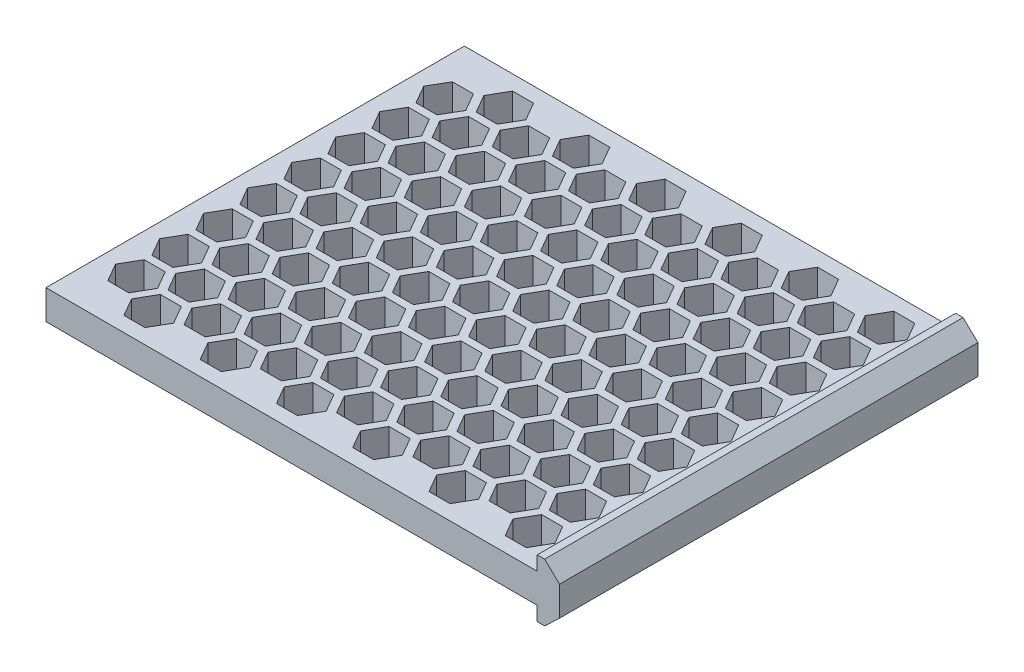
SolidWorks part; units mm, degrees
ref_plane "Front Plane" through (0, 0, 0) normal (0, 0, 1) x (1, 0, 0)
ref_plane "Top Plane" through (0, 0, 0) normal (0, 1, 0) x (1, 0, 0)
ref_plane "Right Plane" through (0, 0, 0) normal (1, 0, 0) x (0, 0, -1)
sketch "Sketch1" plane through (0, 0, 0) normal (0, 0, 1) x (1, 0, 0)
  line L0 (0, 4.05) -> (-140, 4.05)
  line L1 (0, -4.05) -> (-140, -4.05)
  line L2 (-140, -4.05) -> (-140, 4.05)
  line B0 (0, 7.95) -> (2.04, 7.95)
  line B1 (6.1524, 4.048) -> (6.1524, -4.048)
  line B2 (2.04, -7.95) -> (0, -7.95)
  line B3 (0, -7.95) -> (0, 7.95)
  line B4 (2.04, 7.95) -> (6.1524, 4.048)
  line B5 (6.1524, -4.048) -> (2.04, -7.95)
  line B6 (0, 4.05) -> (0, -4.05) construction
  dimension "D1" = 140
sketch_block_instance "Extrusion Profile-2"
sketch_block "Extrusion Profile" parameters "D1"=8.44, "D2"=2.6, "D3"=6, "D4"=16.7, "D6"=5.6686, "D7"=2.0404, "D8"=8.0963, "D9"=15.9, "D5"=2.4157
extrude "Boss-Extrude1" add sketch "Sketch1" along normal blind 115 contours L1 B3 L0 L2 | B2 B5 B1 B4 B0 B3
sketch "Sketch2" plane through (0, 4.05, 0) normal (0, 1, 0) x (1, 0, 0)
  line L0 (-16.1488, -12.65) -> (-14.3301, -11.6) construction
  line L1 (-4.2265, -9.1) -> (-7.1132, -4.1)
  line L2 (-7.1132, -4.1) -> (-12.8868, -4.1)
  line L3 (-12.8868, -4.1) -> (-15.7735, -9.1)
  line L4 (-15.7735, -9.1) -> (-12.8868, -14.1)
  line L5 (-12.8868, -14.1) -> (-7.1132, -14.1)
  line L6 (-7.1132, -14.1) -> (-4.2265, -9.1)
  line L7 (0, -115) -> (0, 0) construction
  line L8 (-4.2265, -21.2) -> (-7.1132, -16.2)
  line L9 (-7.1132, -16.2) -> (-12.8868, -16.2)
  line L10 (-12.8868, -16.2) -> (-15.7735, -21.2)
  line L11 (-15.7735, -21.2) -> (-12.8868, -26.2)
  line L12 (-12.8868, -26.2) -> (-7.1132, -26.2)
  line L13 (-7.1132, -26.2) -> (-4.2265, -21.2)
  line L14 (-4.2265, -33.3) -> (-7.1132, -28.3)
  line L15 (-7.1132, -28.3) -> (-12.8868, -28.3)
  line L16 (-12.8868, -28.3) -> (-15.7735, -33.3)
  line L17 (-15.7735, -33.3) -> (-12.8868, -38.3)
  line L18 (-12.8868, -38.3) -> (-7.1132, -38.3)
  line L19 (-7.1132, -38.3) -> (-4.2265, -33.3)
  line L20 (-4.2265, -45.4) -> (-7.1132, -40.4)
  line L21 (-7.1132, -40.4) -> (-12.8868, -40.4)
  line L22 (-12.8868, -40.4) -> (-15.7735, -45.4)
  line L23 (-15.7735, -45.4) -> (-12.8868, -50.4)
  line L24 (-12.8868, -50.4) -> (-7.1132, -50.4)
  line L25 (-7.1132, -50.4) -> (-4.2265, -45.4)
  line L26 (-4.2265, -57.5) -> (-7.1132, -52.5)
  line L27 (-7.1132, -52.5) -> (-12.8868, -52.5)
  line L28 (-12.8868, -52.5) -> (-15.7735, -57.5)
  line L29 (-15.7735, -57.5) -> (-12.8868, -62.5)
  line L30 (-12.8868, -62.5) -> (-7.1132, -62.5)
  line L31 (-7.1132, -62.5) -> (-4.2265, -57.5)
  line L32 (-4.2265, -69.6) -> (-7.1132, -64.6)
  line L33 (-7.1132, -64.6) -> (-12.8868, -64.6)
  line L34 (-12.8868, -64.6) -> (-15.7735, -69.6)
  line L35 (-15.7735, -69.6) -> (-12.8868, -74.6)
  line L36 (-12.8868, -74.6) -> (-7.1132, -74.6)
  line L37 (-7.1132, -74.6) -> (-4.2265, -69.6)
  line L38 (-4.2265, -81.7) -> (-7.1132, -76.7)
  line L39 (-7.1132, -76.7) -> (-12.8868, -76.7)
  line L40 (-12.8868, -76.7) -> (-15.7735, -81.7)
  line L41 (-15.7735, -81.7) -> (-12.8868, -86.7)
  line L42 (-12.8868, -86.7) -> (-7.1132, -86.7)
  line L43 (-7.1132, -86.7) -> (-4.2265, -81.7)
  line L44 (-4.2265, -93.8) -> (-7.1132, -88.8)
  line L45 (-7.1132, -88.8) -> (-12.8868, -88.8)
  line L46 (-12.8868, -88.8) -> (-15.7735, -93.8)
  line L47 (-15.7735, -93.8) -> (-12.8868, -98.8)
  line L48 (-12.8868, -98.8) -> (-7.1132, -98.8)
  line L49 (-7.1132, -98.8) -> (-4.2265, -93.8)
  line L50 (-4.2265, -105.9) -> (-7.1132, -100.9)
  line L51 (-7.1132, -100.9) -> (-12.8868, -100.9)
  line L52 (-12.8868, -100.9) -> (-15.7735, -105.9)
  line L53 (-15.7735, -105.9) -> (-12.8868, -110.9)
  line L54 (-12.8868, -110.9) -> (-7.1132, -110.9)
  line L55 (-7.1132, -110.9) -> (-4.2265, -105.9)
  line L56 (-14.7054, -15.15) -> (-17.5922, -10.15)
  line L57 (-17.5922, -10.15) -> (-23.3657, -10.15)
  line L58 (-23.3657, -10.15) -> (-26.2524, -15.15)
  line L59 (-10, -4.1) -> (-10, 0) construction
  line L60 (0, 0) -> (-140, 0) construction
  line L61 (-10, -110.9) -> (-10, -115) construction
  line L62 (-26.2524, -15.15) -> (-23.3657, -20.15)
  line L69 (-4.2265, -118) -> (-7.1132, -113) [skipped]
  line L70 (-7.1132, -113) -> (-12.8868, -113) [skipped]
  line L71 (-12.8868, -113) -> (-15.7735, -118) [skipped]
  line L72 (-15.7735, -118) -> (-12.8868, -123) [skipped]
  line L73 (-12.8868, -123) -> (-7.1132, -123) [skipped]
  line L74 (-7.1132, -123) -> (-4.2265, -118) [skipped]
  line L75 (0, -115) -> (-140, -115) construction
  line L76 (-23.3657, -20.15) -> (-17.5922, -20.15)
  line L77 (-17.5922, -20.15) -> (-14.7054, -15.15)
  line L79 (-16.1488, -17.65) -> (-14.3301, -18.7) construction
  line L81 (-10, -14.1) -> (-10, -16.2) construction
  line L83 (-14.7054, -27.25) -> (-17.5922, -22.25)
  line L84 (-17.5922, -22.25) -> (-23.3657, -22.25)
  line L85 (-23.3657, -22.25) -> (-26.2524, -27.25)
  line L86 (-26.2524, -27.25) -> (-23.3657, -32.25)
  line L87 (-23.3657, -32.25) -> (-17.5922, -32.25)
  line L88 (-17.5922, -32.25) -> (-14.7054, -27.25)
  line L89 (-14.7054, -39.35) -> (-17.5922, -34.35)
  line L90 (-17.5922, -34.35) -> (-23.3657, -34.35)
  line L91 (-23.3657, -34.35) -> (-26.2524, -39.35)
  line L92 (-26.2524, -39.35) -> (-23.3657, -44.35)
  line L93 (-23.3657, -44.35) -> (-17.5922, -44.35)
  line L94 (-17.5922, -44.35) -> (-14.7054, -39.35)
  line L95 (-14.7054, -51.45) -> (-17.5922, -46.45)
  line L96 (-17.5922, -46.45) -> (-23.3657, -46.45)
  line L97 (-23.3657, -46.45) -> (-26.2524, -51.45)
  line L98 (-26.2524, -51.45) -> (-23.3657, -56.45)
  line L99 (-23.3657, -56.45) -> (-17.5922, -56.45)
  line L100 (-17.5922, -56.45) -> (-14.7054, -51.45)
  line L101 (-14.7054, -63.55) -> (-17.5922, -58.55)
  line L102 (-17.5922, -58.55) -> (-23.3657, -58.55)
  line L103 (-23.3657, -58.55) -> (-26.2524, -63.55)
  line L104 (-26.2524, -63.55) -> (-23.3657, -68.55)
  line L105 (-23.3657, -68.55) -> (-17.5922, -68.55)
  line L106 (-17.5922, -68.55) -> (-14.7054, -63.55)
  line L107 (-14.7054, -75.65) -> (-17.5922, -70.65)
  line L108 (-17.5922, -70.65) -> (-23.3657, -70.65)
  line L109 (-23.3657, -70.65) -> (-26.2524, -75.65)
  line L110 (-26.2524, -75.65) -> (-23.3657, -80.65)
  line L111 (-23.3657, -80.65) -> (-17.5922, -80.65)
  line L112 (-17.5922, -80.65) -> (-14.7054, -75.65)
  line L113 (-14.7054, -87.75) -> (-17.5922, -82.75)
  line L114 (-17.5922, -82.75) -> (-23.3657, -82.75)
  line L115 (-23.3657, -82.75) -> (-26.2524, -87.75)
  line L116 (-26.2524, -87.75) -> (-23.3657, -92.75)
  line L117 (-23.3657, -92.75) -> (-17.5922, -92.75)
  line L118 (-17.5922, -92.75) -> (-14.7054, -87.75)
  line L119 (-14.7054, -99.85) -> (-17.5922, -94.85)
  line L120 (-17.5922, -94.85) -> (-23.3657, -94.85)
  line L121 (-23.3657, -94.85) -> (-26.2524, -99.85)
  line L122 (-26.2524, -99.85) -> (-23.3657, -104.85)
  line L123 (-23.3657, -104.85) -> (-17.5922, -104.85)
  line L124 (-17.5922, -104.85) -> (-14.7054, -99.85)
  line L125 (-14.7054, -15.15) -> (-14.7054, -27.25) construction
  line L126 (-25.1843, -9.1) -> (-28.0711, -4.1)
  line L127 (-28.0711, -4.1) -> (-33.8446, -4.1)
  line L128 (-33.8446, -4.1) -> (-36.7313, -9.1)
  line L129 (-36.7313, -9.1) -> (-33.8446, -14.1)
  line L130 (-33.8446, -14.1) -> (-28.0711, -14.1)
  line L131 (-28.0711, -14.1) -> (-25.1843, -9.1)
  line L132 (-25.1843, -21.2) -> (-28.0711, -16.2)
  line L133 (-28.0711, -16.2) -> (-33.8446, -16.2)
  line L134 (-33.8446, -16.2) -> (-36.7313, -21.2)
  line L135 (-36.7313, -21.2) -> (-33.8446, -26.2)
  line L136 (-33.8446, -26.2) -> (-28.0711, -26.2)
  line L137 (-28.0711, -26.2) -> (-25.1843, -21.2)
  line L138 (-25.1843, -33.3) -> (-28.0711, -28.3)
  line L139 (-28.0711, -28.3) -> (-33.8446, -28.3)
  line L140 (-33.8446, -28.3) -> (-36.7313, -33.3)
  line L141 (-36.7313, -33.3) -> (-33.8446, -38.3)
  line L142 (-33.8446, -38.3) -> (-28.0711, -38.3)
  line L143 (-28.0711, -38.3) -> (-25.1843, -33.3)
  line L144 (-25.1843, -45.4) -> (-28.0711, -40.4)
  line L145 (-28.0711, -40.4) -> (-33.8446, -40.4)
  line L146 (-33.8446, -40.4) -> (-36.7313, -45.4)
  line L147 (-36.7313, -45.4) -> (-33.8446, -50.4)
  line L148 (-33.8446, -50.4) -> (-28.0711, -50.4)
  line L149 (-28.0711, -50.4) -> (-25.1843, -45.4)
  line L150 (-25.1843, -57.5) -> (-28.0711, -52.5)
  line L151 (-28.0711, -52.5) -> (-33.8446, -52.5)
  line L152 (-33.8446, -52.5) -> (-36.7313, -57.5)
  line L153 (-36.7313, -57.5) -> (-33.8446, -62.5)
  line L154 (-33.8446, -62.5) -> (-28.0711, -62.5)
  line L155 (-28.0711, -62.5) -> (-25.1843, -57.5)
  line L156 (-25.1843, -69.6) -> (-28.0711, -64.6)
  line L157 (-28.0711, -64.6) -> (-33.8446, -64.6)
  line L158 (-33.8446, -64.6) -> (-36.7313, -69.6)
  line L159 (-36.7313, -69.6) -> (-33.8446, -74.6)
  line L160 (-33.8446, -74.6) -> (-28.0711, -74.6)
  line L161 (-28.0711, -74.6) -> (-25.1843, -69.6)
  line L162 (-25.1843, -81.7) -> (-28.0711, -76.7)
  line L163 (-28.0711, -76.7) -> (-33.8446, -76.7)
  line L164 (-33.8446, -76.7) -> (-36.7313, -81.7)
  line L165 (-36.7313, -81.7) -> (-33.8446, -86.7)
  line L166 (-33.8446, -86.7) -> (-28.0711, -86.7)
  line L167 (-28.0711, -86.7) -> (-25.1843, -81.7)
  line L168 (-25.1843, -93.8) -> (-28.0711, -88.8)
  line L169 (-28.0711, -88.8) -> (-33.8446, -88.8)
  line L170 (-33.8446, -88.8) -> (-36.7313, -93.8)
  line L171 (-36.7313, -93.8) -> (-33.8446, -98.8)
  line L172 (-33.8446, -98.8) -> (-28.0711, -98.8)
  line L173 (-28.0711, -98.8) -> (-25.1843, -93.8)
  line L174 (-25.1843, -105.9) -> (-28.0711, -100.9)
  line L175 (-28.0711, -100.9) -> (-33.8446, -100.9)
  line L176 (-33.8446, -100.9) -> (-36.7313, -105.9)
  line L177 (-36.7313, -105.9) -> (-33.8446, -110.9)
  line L178 (-33.8446, -110.9) -> (-28.0711, -110.9)
  line L179 (-28.0711, -110.9) -> (-25.1843, -105.9)
  line L180 (-35.6632, -15.15) -> (-38.55, -10.15)
  line L181 (-38.55, -10.15) -> (-44.3235, -10.15)
  line L182 (-44.3235, -10.15) -> (-47.2102, -15.15)
  line L183 (-47.2102, -15.15) -> (-44.3235, -20.15)
  line L184 (-44.3235, -20.15) -> (-38.55, -20.15)
  line L185 (-38.55, -20.15) -> (-35.6632, -15.15)
  line L186 (-35.6632, -27.25) -> (-38.55, -22.25)
  line L187 (-38.55, -22.25) -> (-44.3235, -22.25)
  line L188 (-44.3235, -22.25) -> (-47.2102, -27.25)
  line L189 (-47.2102, -27.25) -> (-44.3235, -32.25)
  line L190 (-44.3235, -32.25) -> (-38.55, -32.25)
  line L191 (-38.55, -32.25) -> (-35.6632, -27.25)
  line L192 (-35.6632, -39.35) -> (-38.55, -34.35)
  line L193 (-38.55, -34.35) -> (-44.3235, -34.35)
  line L194 (-44.3235, -34.35) -> (-47.2102, -39.35)
  line L195 (-47.2102, -39.35) -> (-44.3235, -44.35)
  line L196 (-44.3235, -44.35) -> (-38.55, -44.35)
  line L197 (-38.55, -44.35) -> (-35.6632, -39.35)
  line L198 (-35.6632, -51.45) -> (-38.55, -46.45)
  line L199 (-38.55, -46.45) -> (-44.3235, -46.45)
  line L200 (-44.3235, -46.45) -> (-47.2102, -51.45)
  line L201 (-47.2102, -51.45) -> (-44.3235, -56.45)
  line L202 (-44.3235, -56.45) -> (-38.55, -56.45)
  line L203 (-38.55, -56.45) -> (-35.6632, -51.45)
  line L204 (-35.6632, -63.55) -> (-38.55, -58.55)
  line L205 (-38.55, -58.55) -> (-44.3235, -58.55)
  line L206 (-44.3235, -58.55) -> (-47.2102, -63.55)
  line L207 (-47.2102, -63.55) -> (-44.3235, -68.55)
  line L208 (-44.3235, -68.55) -> (-38.55, -68.55)
  line L209 (-38.55, -68.55) -> (-35.6632, -63.55)
  line L210 (-35.6632, -75.65) -> (-38.55, -70.65)
  line L211 (-38.55, -70.65) -> (-44.3235, -70.65)
  line L212 (-44.3235, -70.65) -> (-47.2102, -75.65)
  line L213 (-47.2102, -75.65) -> (-44.3235, -80.65)
  line L214 (-44.3235, -80.65) -> (-38.55, -80.65)
  line L215 (-38.55, -80.65) -> (-35.6632, -75.65)
  line L216 (-35.6632, -87.75) -> (-38.55, -82.75)
  line L217 (-38.55, -82.75) -> (-44.3235, -82.75)
  line L218 (-44.3235, -82.75) -> (-47.2102, -87.75)
  line L219 (-47.2102, -87.75) -> (-44.3235, -92.75)
  line L220 (-44.3235, -92.75) -> (-38.55, -92.75)
  line L221 (-38.55, -92.75) -> (-35.6632, -87.75)
  line L222 (-35.6632, -99.85) -> (-38.55, -94.85)
  line L223 (-38.55, -94.85) -> (-44.3235, -94.85)
  line L224 (-44.3235, -94.85) -> (-47.2102, -99.85)
  line L225 (-47.2102, -99.85) -> (-44.3235, -104.85)
  line L226 (-44.3235, -104.85) -> (-38.55, -104.85)
  line L227 (-38.55, -104.85) -> (-35.6632, -99.85)
  line L228 (-37.1066, -12.65) -> (-35.2879, -11.6) construction
  line L229 (-30.9578, -4.1) -> (-30.9578, 0) construction
  line L230 (-30.9578, -110.9) -> (-30.9578, -115) construction
  line L231 (-37.1066, -17.65) -> (-35.2879, -18.7) construction
  line L232 (-30.9578, -15.15) -> (-30.9578, -14.1)
  line L233 (-35.6632, -15.15) -> (-35.6632, -27.25) construction
  line L234 (-46.1421, -9.1) -> (-49.0289, -4.1)
  line L235 (-49.0289, -4.1) -> (-54.8024, -4.1)
  line L236 (-54.8024, -4.1) -> (-57.6891, -9.1)
  line L237 (-57.6891, -9.1) -> (-54.8024, -14.1)
  line L238 (-54.8024, -14.1) -> (-49.0289, -14.1)
  line L239 (-49.0289, -14.1) -> (-46.1421, -9.1)
  line L240 (-46.1421, -21.2) -> (-49.0289, -16.2)
  line L241 (-49.0289, -16.2) -> (-54.8024, -16.2)
  line L242 (-54.8024, -16.2) -> (-57.6891, -21.2)
  line L243 (-57.6891, -21.2) -> (-54.8024, -26.2)
  line L244 (-54.8024, -26.2) -> (-49.0289, -26.2)
  line L245 (-49.0289, -26.2) -> (-46.1421, -21.2)
  line L246 (-46.1421, -33.3) -> (-49.0289, -28.3)
  line L247 (-49.0289, -28.3) -> (-54.8024, -28.3)
  line L248 (-54.8024, -28.3) -> (-57.6891, -33.3)
  line L249 (-57.6891, -33.3) -> (-54.8024, -38.3)
  line L250 (-54.8024, -38.3) -> (-49.0289, -38.3)
  line L251 (-49.0289, -38.3) -> (-46.1421, -33.3)
  line L252 (-46.1421, -45.4) -> (-49.0289, -40.4)
  line L253 (-49.0289, -40.4) -> (-54.8024, -40.4)
  line L254 (-54.8024, -40.4) -> (-57.6891, -45.4)
  line L255 (-57.6891, -45.4) -> (-54.8024, -50.4)
  line L256 (-54.8024, -50.4) -> (-49.0289, -50.4)
  line L257 (-49.0289, -50.4) -> (-46.1421, -45.4)
  line L258 (-46.1421, -57.5) -> (-49.0289, -52.5)
  line L259 (-49.0289, -52.5) -> (-54.8024, -52.5)
  line L260 (-54.8024, -52.5) -> (-57.6891, -57.5)
  line L261 (-57.6891, -57.5) -> (-54.8024, -62.5)
  line L262 (-54.8024, -62.5) -> (-49.0289, -62.5)
  line L263 (-49.0289, -62.5) -> (-46.1421, -57.5)
  line L264 (-46.1421, -69.6) -> (-49.0289, -64.6)
  line L265 (-49.0289, -64.6) -> (-54.8024, -64.6)
  line L266 (-54.8024, -64.6) -> (-57.6891, -69.6)
  line L267 (-57.6891, -69.6) -> (-54.8024, -74.6)
  line L268 (-54.8024, -74.6) -> (-49.0289, -74.6)
  line L269 (-49.0289, -74.6) -> (-46.1421, -69.6)
  line L270 (-46.1421, -81.7) -> (-49.0289, -76.7)
  line L271 (-49.0289, -76.7) -> (-54.8024, -76.7)
  line L272 (-54.8024, -76.7) -> (-57.6891, -81.7)
  line L273 (-57.6891, -81.7) -> (-54.8024, -86.7)
  line L274 (-54.8024, -86.7) -> (-49.0289, -86.7)
  line L275 (-49.0289, -86.7) -> (-46.1421, -81.7)
  line L276 (-46.1421, -93.8) -> (-49.0289, -88.8)
  line L277 (-49.0289, -88.8) -> (-54.8024, -88.8)
  line L278 (-54.8024, -88.8) -> (-57.6891, -93.8)
  line L279 (-57.6891, -93.8) -> (-54.8024, -98.8)
  line L280 (-54.8024, -98.8) -> (-49.0289, -98.8)
  line L281 (-49.0289, -98.8) -> (-46.1421, -93.8)
  line L282 (-46.1421, -105.9) -> (-49.0289, -100.9)
  line L283 (-49.0289, -100.9) -> (-54.8024, -100.9)
  line L284 (-54.8024, -100.9) -> (-57.6891, -105.9)
  line L285 (-57.6891, -105.9) -> (-54.8024, -110.9)
  line L286 (-54.8024, -110.9) -> (-49.0289, -110.9)
  line L287 (-49.0289, -110.9) -> (-46.1421, -105.9)
  line L288 (-56.621, -15.15) -> (-59.5078, -10.15)
  line L289 (-59.5078, -10.15) -> (-65.2813, -10.15)
  line L290 (-65.2813, -10.15) -> (-68.168, -15.15)
  line L291 (-68.168, -15.15) -> (-65.2813, -20.15)
  line L292 (-65.2813, -20.15) -> (-59.5078, -20.15)
  line L293 (-59.5078, -20.15) -> (-56.621, -15.15)
  line L294 (-56.621, -27.25) -> (-59.5078, -22.25)
  line L295 (-59.5078, -22.25) -> (-65.2813, -22.25)
  line L296 (-65.2813, -22.25) -> (-68.168, -27.25)
  line L297 (-68.168, -27.25) -> (-65.2813, -32.25)
  line L298 (-65.2813, -32.25) -> (-59.5078, -32.25)
  line L299 (-59.5078, -32.25) -> (-56.621, -27.25)
  line L300 (-56.621, -39.35) -> (-59.5078, -34.35)
  line L301 (-59.5078, -34.35) -> (-65.2813, -34.35)
  line L302 (-65.2813, -34.35) -> (-68.168, -39.35)
  line L303 (-68.168, -39.35) -> (-65.2813, -44.35)
  line L304 (-65.2813, -44.35) -> (-59.5078, -44.35)
  line L305 (-59.5078, -44.35) -> (-56.621, -39.35)
  line L306 (-56.621, -51.45) -> (-59.5078, -46.45)
  line L307 (-59.5078, -46.45) -> (-65.2813, -46.45)
  line L308 (-65.2813, -46.45) -> (-68.168, -51.45)
  line L309 (-68.168, -51.45) -> (-65.2813, -56.45)
  line L310 (-65.2813, -56.45) -> (-59.5078, -56.45)
  line L311 (-59.5078, -56.45) -> (-56.621, -51.45)
  line L312 (-56.621, -63.55) -> (-59.5078, -58.55)
  line L313 (-59.5078, -58.55) -> (-65.2813, -58.55)
  line L314 (-65.2813, -58.55) -> (-68.168, -63.55)
  line L315 (-68.168, -63.55) -> (-65.2813, -68.55)
  line L316 (-65.2813, -68.55) -> (-59.5078, -68.55)
  line L317 (-59.5078, -68.55) -> (-56.621, -63.55)
  line L318 (-56.621, -75.65) -> (-59.5078, -70.65)
  line L319 (-59.5078, -70.65) -> (-65.2813, -70.65)
  line L320 (-65.2813, -70.65) -> (-68.168, -75.65)
  line L321 (-68.168, -75.65) -> (-65.2813, -80.65)
  line L322 (-65.2813, -80.65) -> (-59.5078, -80.65)
  line L323 (-59.5078, -80.65) -> (-56.621, -75.65)
  line L324 (-56.621, -87.75) -> (-59.5078, -82.75)
  line L325 (-59.5078, -82.75) -> (-65.2813, -82.75)
  line L326 (-65.2813, -82.75) -> (-68.168, -87.75)
  line L327 (-68.168, -87.75) -> (-65.2813, -92.75)
  line L328 (-65.2813, -92.75) -> (-59.5078, -92.75)
  line L329 (-59.5078, -92.75) -> (-56.621, -87.75)
  line L330 (-56.621, -99.85) -> (-59.5078, -94.85)
  line L331 (-59.5078, -94.85) -> (-65.2813, -94.85)
  line L332 (-65.2813, -94.85) -> (-68.168, -99.85)
  line L333 (-68.168, -99.85) -> (-65.2813, -104.85)
  line L334 (-65.2813, -104.85) -> (-59.5078, -104.85)
  line L335 (-59.5078, -104.85) -> (-56.621, -99.85)
  line L336 (-58.0644, -12.65) -> (-56.2458, -11.6) construction
  line L337 (-51.9156, -4.1) -> (-51.9156, 0) construction
  line L338 (-51.9156, -110.9) -> (-51.9156, -115) construction
  line L339 (-58.0644, -17.65) -> (-56.2458, -18.7) construction
  line L340 (-51.9156, -14.1) -> (-51.9156, -16.2) construction
  line L341 (-56.621, -15.15) -> (-56.621, -27.25) construction
  line L342 (-67.0999, -9.1) -> (-69.9867, -4.1)
  line L343 (-69.9867, -4.1) -> (-75.7602, -4.1)
  line L344 (-75.7602, -4.1) -> (-78.6469, -9.1)
  line L345 (-78.6469, -9.1) -> (-75.7602, -14.1)
  line L346 (-75.7602, -14.1) -> (-69.9867, -14.1)
  line L347 (-69.9867, -14.1) -> (-67.0999, -9.1)
  line L348 (-67.0999, -21.2) -> (-69.9867, -16.2)
  line L349 (-69.9867, -16.2) -> (-75.7602, -16.2)
  line L350 (-75.7602, -16.2) -> (-78.6469, -21.2)
  line L351 (-78.6469, -21.2) -> (-75.7602, -26.2)
  line L352 (-75.7602, -26.2) -> (-69.9867, -26.2)
  line L353 (-69.9867, -26.2) -> (-67.0999, -21.2)
  line L354 (-67.0999, -33.3) -> (-69.9867, -28.3)
  line L355 (-69.9867, -28.3) -> (-75.7602, -28.3)
  line L356 (-75.7602, -28.3) -> (-78.6469, -33.3)
  line L357 (-78.6469, -33.3) -> (-75.7602, -38.3)
  line L358 (-75.7602, -38.3) -> (-69.9867, -38.3)
  line L359 (-69.9867, -38.3) -> (-67.0999, -33.3)
  line L360 (-67.0999, -45.4) -> (-69.9867, -40.4)
  line L361 (-69.9867, -40.4) -> (-75.7602, -40.4)
  line L362 (-75.7602, -40.4) -> (-78.6469, -45.4)
  line L363 (-78.6469, -45.4) -> (-75.7602, -50.4)
  line L364 (-75.7602, -50.4) -> (-69.9867, -50.4)
  line L365 (-69.9867, -50.4) -> (-67.0999, -45.4)
  line L366 (-67.0999, -57.5) -> (-69.9867, -52.5)
  line L367 (-69.9867, -52.5) -> (-75.7602, -52.5)
  line L368 (-75.7602, -52.5) -> (-78.6469, -57.5)
  line L369 (-78.6469, -57.5) -> (-75.7602, -62.5)
  line L370 (-75.7602, -62.5) -> (-69.9867, -62.5)
  line L371 (-69.9867, -62.5) -> (-67.0999, -57.5)
  line L372 (-67.0999, -69.6) -> (-69.9867, -64.6)
  line L373 (-69.9867, -64.6) -> (-75.7602, -64.6)
  line L374 (-75.7602, -64.6) -> (-78.6469, -69.6)
  line L375 (-78.6469, -69.6) -> (-75.7602, -74.6)
  line L376 (-75.7602, -74.6) -> (-69.9867, -74.6)
  line L377 (-69.9867, -74.6) -> (-67.0999, -69.6)
  line L378 (-67.0999, -81.7) -> (-69.9867, -76.7)
  line L379 (-69.9867, -76.7) -> (-75.7602, -76.7)
  line L380 (-75.7602, -76.7) -> (-78.6469, -81.7)
  line L381 (-78.6469, -81.7) -> (-75.7602, -86.7)
  line L382 (-75.7602, -86.7) -> (-69.9867, -86.7)
  line L383 (-69.9867, -86.7) -> (-67.0999, -81.7)
  line L384 (-67.0999, -93.8) -> (-69.9867, -88.8)
  line L385 (-69.9867, -88.8) -> (-75.7602, -88.8)
  line L386 (-75.7602, -88.8) -> (-78.6469, -93.8)
  line L387 (-78.6469, -93.8) -> (-75.7602, -98.8)
  line L388 (-75.7602, -98.8) -> (-69.9867, -98.8)
  line L389 (-69.9867, -98.8) -> (-67.0999, -93.8)
  line L390 (-67.0999, -105.9) -> (-69.9867, -100.9)
  line L391 (-69.9867, -100.9) -> (-75.7602, -100.9)
  line L392 (-75.7602, -100.9) -> (-78.6469, -105.9)
  line L393 (-78.6469, -105.9) -> (-75.7602, -110.9)
  line L394 (-75.7602, -110.9) -> (-69.9867, -110.9)
  line L395 (-69.9867, -110.9) -> (-67.0999, -105.9)
  line L396 (-77.5788, -15.15) -> (-80.4656, -10.15)
  line L397 (-80.4656, -10.15) -> (-86.2391, -10.15)
  line L398 (-86.2391, -10.15) -> (-89.1259, -15.15)
  line L399 (-89.1259, -15.15) -> (-86.2391, -20.15)
  line L400 (-86.2391, -20.15) -> (-80.4656, -20.15)
  line L401 (-80.4656, -20.15) -> (-77.5788, -15.15)
  line L402 (-77.5788, -27.25) -> (-80.4656, -22.25)
  line L403 (-80.4656, -22.25) -> (-86.2391, -22.25)
  line L404 (-86.2391, -22.25) -> (-89.1259, -27.25)
  line L405 (-89.1259, -27.25) -> (-86.2391, -32.25)
  line L406 (-86.2391, -32.25) -> (-80.4656, -32.25)
  line L407 (-80.4656, -32.25) -> (-77.5788, -27.25)
  line L408 (-77.5788, -39.35) -> (-80.4656, -34.35)
  line L409 (-80.4656, -34.35) -> (-86.2391, -34.35)
  line L410 (-86.2391, -34.35) -> (-89.1259, -39.35)
  line L411 (-89.1259, -39.35) -> (-86.2391, -44.35)
  line L412 (-86.2391, -44.35) -> (-80.4656, -44.35)
  line L413 (-80.4656, -44.35) -> (-77.5788, -39.35)
  line L414 (-77.5788, -51.45) -> (-80.4656, -46.45)
  line L415 (-80.4656, -46.45) -> (-86.2391, -46.45)
  line L416 (-86.2391, -46.45) -> (-89.1259, -51.45)
  line L417 (-89.1259, -51.45) -> (-86.2391, -56.45)
  line L418 (-86.2391, -56.45) -> (-80.4656, -56.45)
  line L419 (-80.4656, -56.45) -> (-77.5788, -51.45)
  line L420 (-77.5788, -63.55) -> (-80.4656, -58.55)
  line L421 (-80.4656, -58.55) -> (-86.2391, -58.55)
  line L422 (-86.2391, -58.55) -> (-89.1259, -63.55)
  line L423 (-89.1259, -63.55) -> (-86.2391, -68.55)
  line L424 (-86.2391, -68.55) -> (-80.4656, -68.55)
  line L425 (-80.4656, -68.55) -> (-77.5788, -63.55)
  line L426 (-77.5788, -75.65) -> (-80.4656, -70.65)
  line L427 (-80.4656, -70.65) -> (-86.2391, -70.65)
  line L428 (-86.2391, -70.65) -> (-89.1259, -75.65)
  line L429 (-89.1259, -75.65) -> (-86.2391, -80.65)
  line L430 (-86.2391, -80.65) -> (-80.4656, -80.65)
  line L431 (-80.4656, -80.65) -> (-77.5788, -75.65)
  line L432 (-77.5788, -87.75) -> (-80.4656, -82.75)
  line L433 (-80.4656, -82.75) -> (-86.2391, -82.75)
  line L434 (-86.2391, -82.75) -> (-89.1259, -87.75)
  line L435 (-89.1259, -87.75) -> (-86.2391, -92.75)
  line L436 (-86.2391, -92.75) -> (-80.4656, -92.75)
  line L437 (-80.4656, -92.75) -> (-77.5788, -87.75)
  line L438 (-77.5788, -99.85) -> (-80.4656, -94.85)
  line L439 (-80.4656, -94.85) -> (-86.2391, -94.85)
  line L440 (-86.2391, -94.85) -> (-89.1259, -99.85)
  line L441 (-89.1259, -99.85) -> (-86.2391, -104.85)
  line L442 (-86.2391, -104.85) -> (-80.4656, -104.85)
  line L443 (-80.4656, -104.85) -> (-77.5788, -99.85)
  line L444 (-79.0222, -12.65) -> (-77.2036, -11.6) construction
  line L445 (-72.8734, -4.1) -> (-72.8734, 0) construction
  line L446 (-72.8734, -110.9) -> (-72.8734, -115) construction
  line L447 (-79.0222, -17.65) -> (-77.2036, -18.7) construction
  line L448 (-72.8734, -14.1) -> (-72.8734, -16.2) construction
  line L449 (-77.5788, -15.15) -> (-77.5788, -27.25) construction
  line L450 (-88.0578, -9.1) -> (-90.9445, -4.1)
  line L451 (-90.9445, -4.1) -> (-96.718, -4.1)
  line L452 (-96.718, -4.1) -> (-99.6048, -9.1)
  line L453 (-99.6048, -9.1) -> (-96.718, -14.1)
  line L454 (-96.718, -14.1) -> (-90.9445, -14.1)
  line L455 (-90.9445, -14.1) -> (-88.0578, -9.1)
  line L456 (-88.0578, -21.2) -> (-90.9445, -16.2)
  line L457 (-90.9445, -16.2) -> (-96.718, -16.2)
  line L458 (-96.718, -16.2) -> (-99.6048, -21.2)
  line L459 (-99.6048, -21.2) -> (-96.718, -26.2)
  line L460 (-96.718, -26.2) -> (-90.9445, -26.2)
  line L461 (-90.9445, -26.2) -> (-88.0578, -21.2)
  line L462 (-88.0578, -33.3) -> (-90.9445, -28.3)
  line L463 (-90.9445, -28.3) -> (-96.718, -28.3)
  line L464 (-96.718, -28.3) -> (-99.6048, -33.3)
  line L465 (-99.6048, -33.3) -> (-96.718, -38.3)
  line L466 (-96.718, -38.3) -> (-90.9445, -38.3)
  line L467 (-90.9445, -38.3) -> (-88.0578, -33.3)
  line L468 (-88.0578, -45.4) -> (-90.9445, -40.4)
  line L469 (-90.9445, -40.4) -> (-96.718, -40.4)
  line L470 (-96.718, -40.4) -> (-99.6048, -45.4)
  line L471 (-99.6048, -45.4) -> (-96.718, -50.4)
  line L472 (-96.718, -50.4) -> (-90.9445, -50.4)
  line L473 (-90.9445, -50.4) -> (-88.0578, -45.4)
  line L474 (-88.0578, -57.5) -> (-90.9445, -52.5)
  line L475 (-90.9445, -52.5) -> (-96.718, -52.5)
  line L476 (-96.718, -52.5) -> (-99.6048, -57.5)
  line L477 (-99.6048, -57.5) -> (-96.718, -62.5)
  line L478 (-96.718, -62.5) -> (-90.9445, -62.5)
  line L479 (-90.9445, -62.5) -> (-88.0578, -57.5)
  line L480 (-88.0578, -69.6) -> (-90.9445, -64.6)
  line L481 (-90.9445, -64.6) -> (-96.718, -64.6)
  line L482 (-96.718, -64.6) -> (-99.6048, -69.6)
  line L483 (-99.6048, -69.6) -> (-96.718, -74.6)
  line L484 (-96.718, -74.6) -> (-90.9445, -74.6)
  line L485 (-90.9445, -74.6) -> (-88.0578, -69.6)
  line L486 (-88.0578, -81.7) -> (-90.9445, -76.7)
  line L487 (-90.9445, -76.7) -> (-96.718, -76.7)
  line L488 (-96.718, -76.7) -> (-99.6048, -81.7)
  line L489 (-99.6048, -81.7) -> (-96.718, -86.7)
  line L490 (-96.718, -86.7) -> (-90.9445, -86.7)
  line L491 (-90.9445, -86.7) -> (-88.0578, -81.7)
  line L492 (-88.0578, -93.8) -> (-90.9445, -88.8)
  line L493 (-90.9445, -88.8) -> (-96.718, -88.8)
  line L494 (-96.718, -88.8) -> (-99.6048, -93.8)
  line L495 (-99.6048, -93.8) -> (-96.718, -98.8)
  line L496 (-96.718, -98.8) -> (-90.9445, -98.8)
  line L497 (-90.9445, -98.8) -> (-88.0578, -93.8)
  line L498 (-88.0578, -105.9) -> (-90.9445, -100.9)
  line L499 (-90.9445, -100.9) -> (-96.718, -100.9)
  line L500 (-96.718, -100.9) -> (-99.6048, -105.9)
  line L501 (-99.6048, -105.9) -> (-96.718, -110.9)
  line L502 (-96.718, -110.9) -> (-90.9445, -110.9)
  line L503 (-90.9445, -110.9) -> (-88.0578, -105.9)
  line L504 (-98.5367, -15.15) -> (-101.4234, -10.15)
  line L505 (-101.4234, -10.15) -> (-107.1969, -10.15)
  line L506 (-107.1969, -10.15) -> (-110.0837, -15.15)
  line L507 (-110.0837, -15.15) -> (-107.1969, -20.15)
  line L508 (-107.1969, -20.15) -> (-101.4234, -20.15)
  line L509 (-101.4234, -20.15) -> (-98.5367, -15.15)
  line L510 (-98.5367, -27.25) -> (-101.4234, -22.25)
  line L511 (-101.4234, -22.25) -> (-107.1969, -22.25)
  line L512 (-107.1969, -22.25) -> (-110.0837, -27.25)
  line L513 (-110.0837, -27.25) -> (-107.1969, -32.25)
  line L514 (-107.1969, -32.25) -> (-101.4234, -32.25)
  line L515 (-101.4234, -32.25) -> (-98.5367, -27.25)
  line L516 (-98.5367, -39.35) -> (-101.4234, -34.35)
  line L517 (-101.4234, -34.35) -> (-107.1969, -34.35)
  line L518 (-107.1969, -34.35) -> (-110.0837, -39.35)
  line L519 (-110.0837, -39.35) -> (-107.1969, -44.35)
  line L520 (-107.1969, -44.35) -> (-101.4234, -44.35)
  line L521 (-101.4234, -44.35) -> (-98.5367, -39.35)
  line L522 (-98.5367, -51.45) -> (-101.4234, -46.45)
  line L523 (-101.4234, -46.45) -> (-107.1969, -46.45)
  line L524 (-107.1969, -46.45) -> (-110.0837, -51.45)
  line L525 (-110.0837, -51.45) -> (-107.1969, -56.45)
  line L526 (-107.1969, -56.45) -> (-101.4234, -56.45)
  line L527 (-101.4234, -56.45) -> (-98.5367, -51.45)
  line L528 (-98.5367, -63.55) -> (-101.4234, -58.55)
  line L529 (-101.4234, -58.55) -> (-107.1969, -58.55)
  line L530 (-107.1969, -58.55) -> (-110.0837, -63.55)
  line L531 (-110.0837, -63.55) -> (-107.1969, -68.55)
  line L532 (-107.1969, -68.55) -> (-101.4234, -68.55)
  line L533 (-101.4234, -68.55) -> (-98.5367, -63.55)
  line L534 (-98.5367, -75.65) -> (-101.4234, -70.65)
  line L535 (-101.4234, -70.65) -> (-107.1969, -70.65)
  line L536 (-107.1969, -70.65) -> (-110.0837, -75.65)
  line L537 (-110.0837, -75.65) -> (-107.1969, -80.65)
  line L538 (-107.1969, -80.65) -> (-101.4234, -80.65)
  line L539 (-101.4234, -80.65) -> (-98.5367, -75.65)
  line L540 (-98.5367, -87.75) -> (-101.4234, -82.75)
  line L541 (-101.4234, -82.75) -> (-107.1969, -82.75)
  line L542 (-107.1969, -82.75) -> (-110.0837, -87.75)
  line L543 (-110.0837, -87.75) -> (-107.1969, -92.75)
  line L544 (-107.1969, -92.75) -> (-101.4234, -92.75)
  line L545 (-101.4234, -92.75) -> (-98.5367, -87.75)
  line L546 (-98.5367, -99.85) -> (-101.4234, -94.85)
  line L547 (-101.4234, -94.85) -> (-107.1969, -94.85)
  line L548 (-107.1969, -94.85) -> (-110.0837, -99.85)
  line L549 (-110.0837, -99.85) -> (-107.1969, -104.85)
  line L550 (-107.1969, -104.85) -> (-101.4234, -104.85)
  line L551 (-101.4234, -104.85) -> (-98.5367, -99.85)
  line L552 (-99.98, -12.65) -> (-98.1614, -11.6) construction
  line L553 (-93.8313, -4.1) -> (-93.8313, 0) construction
  line L554 (-93.8313, -110.9) -> (-93.8313, -115) construction
  line L555 (-99.98, -17.65) -> (-98.1614, -18.7) construction
  line L556 (-93.8313, -14.1) -> (-93.8313, -16.2) construction
  line L557 (-98.5367, -15.15) -> (-98.5367, -27.25) construction
  line L558 (-109.0156, -9.1) -> (-111.9023, -4.1)
  line L559 (-111.9023, -4.1) -> (-117.6758, -4.1)
  line L560 (-117.6758, -4.1) -> (-120.5626, -9.1)
  line L561 (-120.5626, -9.1) -> (-117.6758, -14.1)
  line L562 (-117.6758, -14.1) -> (-111.9023, -14.1)
  line L563 (-111.9023, -14.1) -> (-109.0156, -9.1)
  line L564 (-109.0156, -21.2) -> (-111.9023, -16.2)
  line L565 (-111.9023, -16.2) -> (-117.6758, -16.2)
  line L566 (-117.6758, -16.2) -> (-120.5626, -21.2)
  line L567 (-120.5626, -21.2) -> (-117.6758, -26.2)
  line L568 (-117.6758, -26.2) -> (-111.9023, -26.2)
  line L569 (-111.9023, -26.2) -> (-109.0156, -21.2)
  line L570 (-109.0156, -33.3) -> (-111.9023, -28.3)
  line L571 (-111.9023, -28.3) -> (-117.6758, -28.3)
  line L572 (-117.6758, -28.3) -> (-120.5626, -33.3)
  line L573 (-120.5626, -33.3) -> (-117.6758, -38.3)
  line L574 (-117.6758, -38.3) -> (-111.9023, -38.3)
  line L575 (-111.9023, -38.3) -> (-109.0156, -33.3)
  line L576 (-109.0156, -45.4) -> (-111.9023, -40.4)
  line L577 (-111.9023, -40.4) -> (-117.6758, -40.4)
  line L578 (-117.6758, -40.4) -> (-120.5626, -45.4)
  line L579 (-120.5626, -45.4) -> (-117.6758, -50.4)
  line L580 (-117.6758, -50.4) -> (-111.9023, -50.4)
  line L581 (-111.9023, -50.4) -> (-109.0156, -45.4)
  line L582 (-109.0156, -57.5) -> (-111.9023, -52.5)
  line L583 (-111.9023, -52.5) -> (-117.6758, -52.5)
  line L584 (-117.6758, -52.5) -> (-120.5626, -57.5)
  line L585 (-120.5626, -57.5) -> (-117.6758, -62.5)
  line L586 (-117.6758, -62.5) -> (-111.9023, -62.5)
  line L587 (-111.9023, -62.5) -> (-109.0156, -57.5)
  line L588 (-109.0156, -69.6) -> (-111.9023, -64.6)
  line L589 (-111.9023, -64.6) -> (-117.6758, -64.6)
  line L590 (-117.6758, -64.6) -> (-120.5626, -69.6)
  line L591 (-120.5626, -69.6) -> (-117.6758, -74.6)
  line L592 (-117.6758, -74.6) -> (-111.9023, -74.6)
  line L593 (-111.9023, -74.6) -> (-109.0156, -69.6)
  line L594 (-109.0156, -81.7) -> (-111.9023, -76.7)
  line L595 (-111.9023, -76.7) -> (-117.6758, -76.7)
  line L596 (-117.6758, -76.7) -> (-120.5626, -81.7)
  line L597 (-120.5626, -81.7) -> (-117.6758, -86.7)
  line L598 (-117.6758, -86.7) -> (-111.9023, -86.7)
  line L599 (-111.9023, -86.7) -> (-109.0156, -81.7)
  line L600 (-109.0156, -93.8) -> (-111.9023, -88.8)
  line L601 (-111.9023, -88.8) -> (-117.6758, -88.8)
  line L602 (-117.6758, -88.8) -> (-120.5626, -93.8)
  line L603 (-120.5626, -93.8) -> (-117.6758, -98.8)
  line L604 (-117.6758, -98.8) -> (-111.9023, -98.8)
  line L605 (-111.9023, -98.8) -> (-109.0156, -93.8)
  line L606 (-109.0156, -105.9) -> (-111.9023, -100.9)
  line L607 (-111.9023, -100.9) -> (-117.6758, -100.9)
  line L608 (-117.6758, -100.9) -> (-120.5626, -105.9)
  line L609 (-120.5626, -105.9) -> (-117.6758, -110.9)
  line L610 (-117.6758, -110.9) -> (-111.9023, -110.9)
  line L611 (-111.9023, -110.9) -> (-109.0156, -105.9)
  line L612 (-119.4945, -15.15) -> (-122.3812, -10.15)
  line L613 (-122.3812, -10.15) -> (-128.1547, -10.15)
  line L614 (-128.1547, -10.15) -> (-131.0415, -15.15)
  line L615 (-131.0415, -15.15) -> (-128.1547, -20.15)
  line L616 (-128.1547, -20.15) -> (-122.3812, -20.15)
  line L617 (-122.3812, -20.15) -> (-119.4945, -15.15)
  line L618 (-119.4945, -27.25) -> (-122.3812, -22.25)
  line L619 (-122.3812, -22.25) -> (-128.1547, -22.25)
  line L620 (-128.1547, -22.25) -> (-131.0415, -27.25)
  line L621 (-131.0415, -27.25) -> (-128.1547, -32.25)
  line L622 (-128.1547, -32.25) -> (-122.3812, -32.25)
  line L623 (-122.3812, -32.25) -> (-119.4945, -27.25)
  line L624 (-119.4945, -39.35) -> (-122.3812, -34.35)
  line L625 (-122.3812, -34.35) -> (-128.1547, -34.35)
  line L626 (-128.1547, -34.35) -> (-131.0415, -39.35)
  line L627 (-131.0415, -39.35) -> (-128.1547, -44.35)
  line L628 (-128.1547, -44.35) -> (-122.3812, -44.35)
  line L629 (-122.3812, -44.35) -> (-119.4945, -39.35)
  line L630 (-119.4945, -51.45) -> (-122.3812, -46.45)
  line L631 (-122.3812, -46.45) -> (-128.1547, -46.45)
  line L632 (-128.1547, -46.45) -> (-131.0415, -51.45)
  line L633 (-131.0415, -51.45) -> (-128.1547, -56.45)
  line L634 (-128.1547, -56.45) -> (-122.3812, -56.45)
  line L635 (-122.3812, -56.45) -> (-119.4945, -51.45)
  line L636 (-119.4945, -63.55) -> (-122.3812, -58.55)
  line L637 (-122.3812, -58.55) -> (-128.1547, -58.55)
  line L638 (-128.1547, -58.55) -> (-131.0415, -63.55)
  line L639 (-131.0415, -63.55) -> (-128.1547, -68.55)
  line L640 (-128.1547, -68.55) -> (-122.3812, -68.55)
  line L641 (-122.3812, -68.55) -> (-119.4945, -63.55)
  line L642 (-119.4945, -75.65) -> (-122.3812, -70.65)
  line L643 (-122.3812, -70.65) -> (-128.1547, -70.65)
  line L644 (-128.1547, -70.65) -> (-131.0415, -75.65)
  line L645 (-131.0415, -75.65) -> (-128.1547, -80.65)
  line L646 (-128.1547, -80.65) -> (-122.3812, -80.65)
  line L647 (-122.3812, -80.65) -> (-119.4945, -75.65)
  line L648 (-119.4945, -87.75) -> (-122.3812, -82.75)
  line L649 (-122.3812, -82.75) -> (-128.1547, -82.75)
  line L650 (-128.1547, -82.75) -> (-131.0415, -87.75)
  line L651 (-131.0415, -87.75) -> (-128.1547, -92.75)
  line L652 (-128.1547, -92.75) -> (-122.3812, -92.75)
  line L653 (-122.3812, -92.75) -> (-119.4945, -87.75)
  line L654 (-119.4945, -99.85) -> (-122.3812, -94.85)
  line L655 (-122.3812, -94.85) -> (-128.1547, -94.85)
  line L656 (-128.1547, -94.85) -> (-131.0415, -99.85)
  line L657 (-131.0415, -99.85) -> (-128.1547, -104.85)
  line L658 (-128.1547, -104.85) -> (-122.3812, -104.85)
  line L659 (-122.3812, -104.85) -> (-119.4945, -99.85)
  line L660 (-120.9379, -12.65) -> (-119.1192, -11.6) construction
  line L661 (-114.7891, -4.1) -> (-114.7891, 0) construction
  line L662 (-114.7891, -110.9) -> (-114.7891, -115) construction
  line L663 (-120.9379, -17.65) -> (-119.1192, -18.7) construction
  line L664 (-114.7891, -14.1) -> (-114.7891, -16.2) construction
  line L665 (-119.4945, -15.15) -> (-119.4945, -27.25) construction
  line L774 (-20.4789, -15.15) -> (-10, -15.15) construction
  line L775 (-20.4789, -15.15) -> (-30.9578, -15.15) construction
  line L777 (-30.9578, -14.1) -> (-30.9578, -16.2) construction
  circle A0 centre (-10, -9.1) radius 5 construction
  circle A1 centre (-20.4789, -15.15) radius 5 construction
  circle A2 centre (-30.9578, -9.1) radius 5 construction
  circle A3 centre (-41.4367, -15.15) radius 5 construction
  circle A4 centre (-51.9156, -9.1) radius 5 construction
  circle A5 centre (-62.3945, -15.15) radius 5 construction
  circle A6 centre (-72.8734, -9.1) radius 5 construction
  circle A7 centre (-83.3524, -15.15) radius 5 construction
  circle A8 centre (-93.8313, -9.1) radius 5 construction
  circle A9 centre (-104.3102, -15.15) radius 5 construction
  circle A10 centre (-114.7891, -9.1) radius 5 construction
  circle A11 centre (-125.268, -15.15) radius 5 construction
  dimension "D1" = 10
  dimension "D2" = 12.1
  dimension "D3" = 10
  dimension "D5" = 8
  dimension "D6" = 12.1
  dimension "D7" = 6
  dimension "D4" = 10
extrude "Cut-Extrude3" cut sketch "Sketch2" against normal through all contours L616 L617 L612 L613 L614 L615 | L622 L623 L618 L619 L620 L621 | L628 L629 L624 L625 L626 L627 | L634 L635 L630 L631 L632 L633 | L640 L641 L636 L637 L638 L639 | L646 L647 L642 L643 L644 L645 | L652 L653 L648 L649 L650 L651 | L658 L659 L654 L655 L656 L657 | L610 L611 L606 L607 L608 L609 | L604 L605 L600 L601 L602 L603 | L598 L599 L594 L595 L596 L597 | L592 L593 L588 L589 L590 L591 | L586 L587 L582 L583 L584 L585 | L580 L581 L576 L577 L578 L579 | L574 L575 L570 L571 L572 L573 | L568 L569 L564 L565 L566 L567 | L562 L563 L558 L559 L560 L561 | L508 L509 L504 L505 L506 L507 | L514 L515 L510 L511 L512 L513 | L520 L521 L516 L517 L518 L519 | L526 L527 L522 L523 L524 L525 | L538 L539 L534 L535 L536 L537 | L544 L545 L540 L541 L542 L543 | L550 L551 L546 L547 L548 L549 | L496 L497 L492 L493 L494 L495 | L502 L503 L498 L499 L500 L501 | L490 L491 L486 L487 L488 L489 | L484 L485 L480 L481 L482 L483 | L478 L479 L474 L475 L476 L477 | L472 L473 L468 L469 L470 L471 | L466 L467 L462 L463 L464 L465 | L460 L461 L456 L457 L458 L459 | L454 L455 L450 L451 L452 L453 | L400 L401 L396 L397 L398 L399 | L406 L407 L402 L403 L404 L405 | L412 L413 L408 L409 L410 L411 | L418 L419 L414 L415 L416 L417 | L424 L425 L420 L421 L422 L423 | L430 L431 L426 L427 L428 L429 | L436 L437 L432 L433 L434 L435 | L442 L443 L438 L439 L440 L441 | L394 L395 L390 L391 L392 L393 | L388 L389 L384 L385 L386 L387 | L382 L383 L378 L379 L380 L381 | L376 L377 L372 L373 L374 L375 | L370 L371 L366 L367 L368 L369 | L364 L365 L360 L361 L362 L363 | L358 L359 L354 L355 L356 L357 | L352 L353 L348 L349 L350 L351 | L346 L347 L342 L343 L344 L345 | L292 L293 L288 L289 L290 L291 | L298 L299 L294 L295 L296 L297 | L304 L305 L300 L301 L302 L303 | L310 L311 L306 L307 L308 L309 | L316 L317 L312 L313 L314 L315 | L322 L323 L318 L319 L320 L321 | L328 L329 L324 L325 L326 L327 | L334 L335 L330 L331 L332 L333 | L286 L287 L282 L283 L284 L285 | L280 L281 L276 L277 L278 L279 | L274 L275 L270 L271 L272 L273 | L220 L221 L216 L217 L218 L219 | L214 L215 L210 L211 L212 L213 | L226 L227 L222 L223 L224 L225 | L208 L209 L204 L205 L206 L207 | L262 L263 L258 L259 L260 L261 | L202 L203 L198 L199 L200 L201 | L256 L257 L252 L253 L254 L255 | L196 L197 L192 L193 L194 L195 | L250 L251 L246 L247 L248 L249 | L190 L191 L186 L187 L188 L189 | L244 L245 L240 L241 L242 L243 | L238 L239 L234 L235 L236 L237 | L130 L131 L126 L127 L128 L129 | L136 L137 L132 L133 L134 L135 | L142 L143 L138 L139 L140 L141 | L148 L149 L144 L145 L146 L147 | L154 L155 L150 L151 L152 L153 | L160 L161 L156 L157 L158 L159 | L172 L173 L168 L169 L170 L171 | L178 L179 L174 L175 L176 L177 | L123 L124 L119 L120 L121 L122 | L117 L118 L113 L114 L115 L116 | L111 L112 L107 L108 L109 L110 | L105 L106 L101 L102 L103 L104 | L99 L100 L95 L96 L97 L98 | L87 L88 L83 L84 L85 L86 | L76 L77 L56 L57 L58 L62 | L5 L6 L1 L2 L3 L4 | L12 L13 L8 L9 L10 L11 | L18 L19 L14 L15 L16 L17 | L24 L25 L20 L21 L22 L23 | L30 L31 L26 L27 L28 L29 | L36 L37 L32 L33 L34 L35 | L42 L43 L38 L39 L40 L41 | L48 L49 L44 L45 L46 L47 | L54 L55 L50 L51 L52 L53 | L532 L533 L528 L529 L530 L531 | L268 L269 L264 L265 L266 L267 | L184 L185 L180 L181 L182 L183 | L93 L94 L89 L90 L91 L92 | L166 L167 L162 L163 L164 L165
sketch "Sketch3" plane through (0, 0, 115) normal (0, 0, 1) x (1, 0, 0)
  line L0 (-140, 4.05) -> (-135, 4.05)
  line L1 (0, 4.05) -> (-140, 4.05) construction
  line L2 (-135, 4.05) -> (-135, -4.05)
  line L3 (0, -4.05) -> (-140, -4.05) construction
  line L4 (-135, -4.05) -> (-140, -4.05)
  line L5 (-140, -4.05) -> (-140, 4.05)
  dimension "D1" = 5
extrude "Cut-Extrude4" cut sketch "Sketch3" against normal through all
